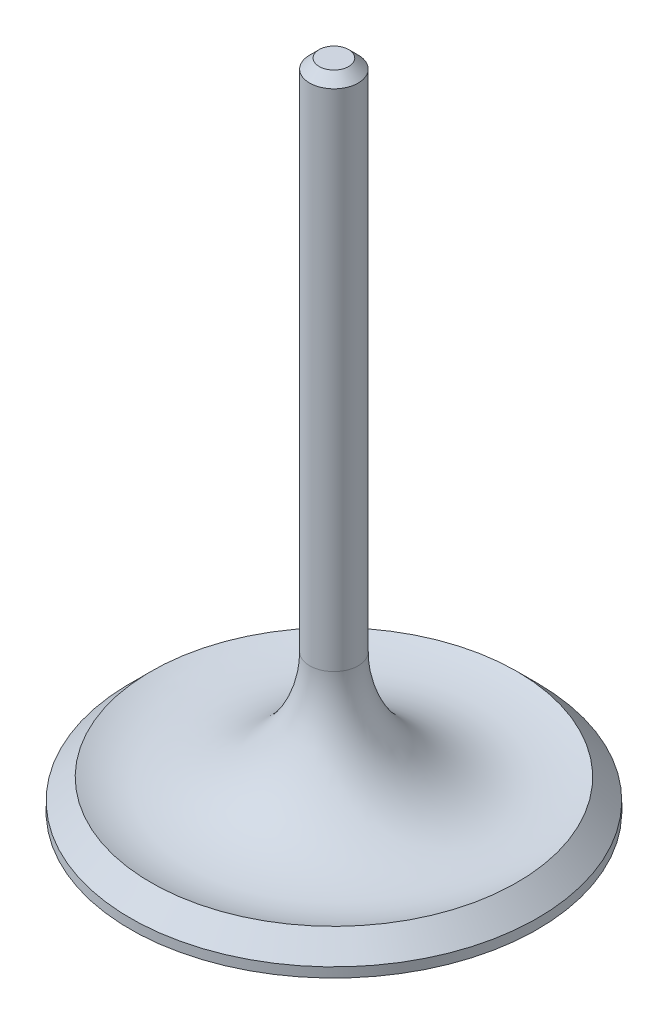
SolidWorks part; units mm, degrees
ref_plane "Plan de face" through (0, 0, 0) normal (0, 0, 1) x (1, 0, 0)
ref_plane "Plan de dessus" through (0, 0, 0) normal (0, 1, 0) x (1, 0, 0)
ref_plane "Plan de droite" through (0, 0, 0) normal (1, 0, 0) x (0, 0, -1)
sketch "Esquisse1" plane through (0, 0, 0) normal (1, 0, 0) x (0, 0, -1)
  line L0 (0, 0) -> (0, 85.55)
  line L1 (0, 85.55) -> (3.18, 85.55)
  line L2 (3.18, 85.55) -> (3.18, 18.1699)
  line L3 (23.9759, 3.9641) -> (26.67, 1.27)
  line L4 (26.67, 1.27) -> (26.67, 0)
  line L5 (26.67, 0) -> (0, 0)
  arc A1 (3.18, 18.1699) -> (23.9759, 3.9641) centre (18.43, 18.1699) ccw
  dimension "D6" = 15.25
  dimension "D1" = 85.55
  dimension "D2" = 3.18
  dimension "D3" = 26.67
  dimension "D4" = 1.27
  dimension "D5" = 3.81
  dimension "D7" = 45
revolve "Révolution1" add sketch "Esquisse1" angle 360 about L0
chamfer "Chanfrein1" distance 1.25 angle 45 1 edges at (0, 85.55, -3.18)
